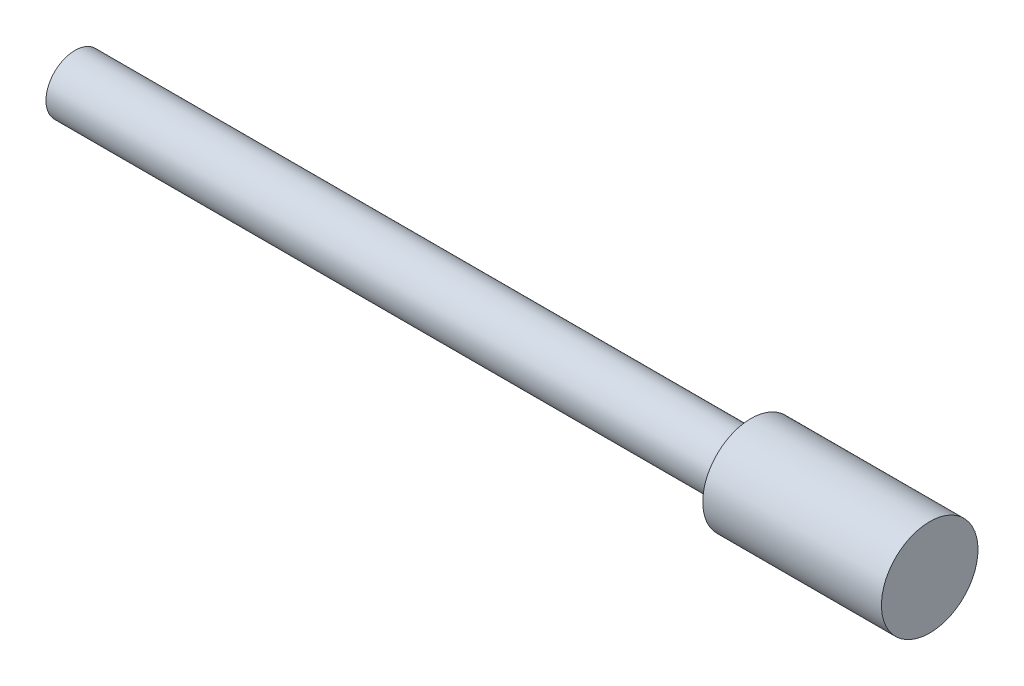
SolidWorks part; units mm, degrees
ref_plane "Front Plane" through (0, 0, 0) normal (0, 0, 1) x (1, 0, 0)
ref_plane "Top Plane" through (0, 0, 0) normal (0, 1, 0) x (1, 0, 0)
ref_plane "Right Plane" through (0, 0, 0) normal (1, 0, 0) x (0, 0, -1)
sketch "Sketch1" plane through (0, 0, 0) normal (1, 0, 0) x (0, 0, -1)
  circle A0 centre (0, 0) radius 6
  dimension "D1" = 12
extrude "Boss-Extrude1" add sketch "Sketch1" along normal blind 140
sketch "Sketch2" plane through (140, 0, 0) normal (1, 0, 0) x (0, 0, -1)
  circle A0 centre (0, 0) radius 10
  dimension "D1" = 20
extrude "Boss-Extrude2" add sketch "Sketch2" along normal blind 37
